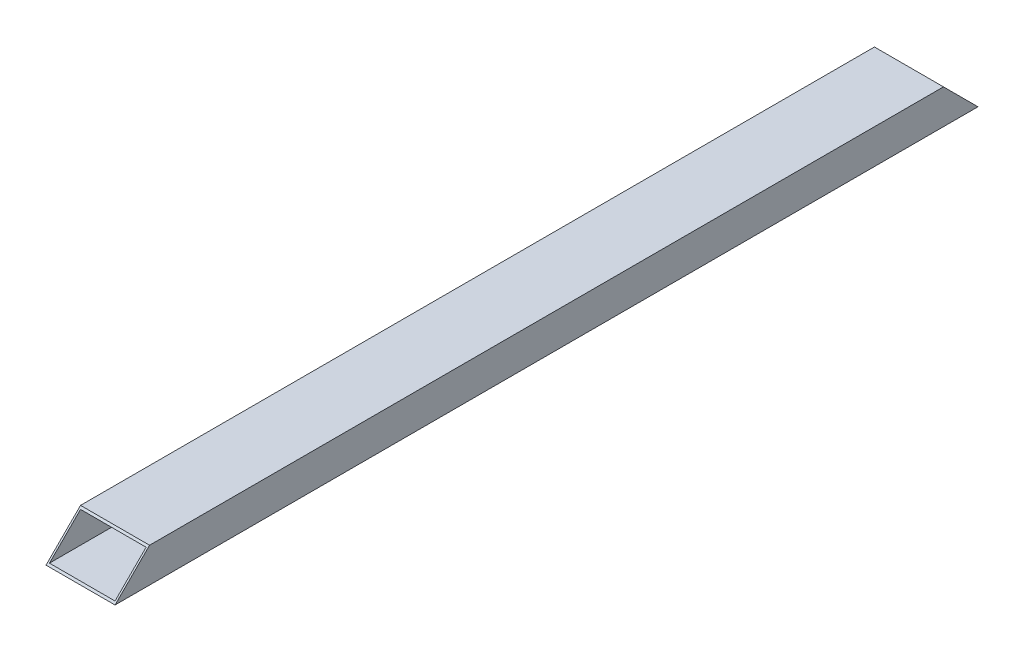
SolidWorks part; units mm, degrees
ref_plane "Front Plane" through (0, 0, 0) normal (0, 0, 1) x (1, 0, 0)
ref_plane "Top Plane" through (0, 0, 0) normal (0, 1, 0) x (1, 0, 0)
ref_plane "Right Plane" through (0, 0, 0) normal (1, 0, 0) x (0, 0, -1)
sketch "Sketch1" plane through (0, 0, 0) normal (0, 0, 1) x (1, 0, 0)
  line L0 (-27.5574, 0) -> (38.5818, 0) construction
  line L1 (0, 18.8259) -> (0, -17.5693) construction
  line L5 (20, -8) -> (-20, -8)
  line L8 (-20, -8) -> (-20, 12)
  line L9 (20, -8) -> (20, 12)
  line L10 (-20, 12) -> (20, 12)
  point P7 (0, -8)
  dimension "D1" = 40
  dimension "D2" = 40
  dimension "D3" = 20
extrude "Boss-Extrude1" add sketch "Sketch1" along normal blind 500
sketch "Sketch3" plane through (0, 0, 500) normal (0, 0, 1) x (1, 0, 0)
  line L16 (-19, -7) -> (19, -7)
  line L17 (-19, 11) -> (-19, -7)
  line L18 (19, -7) -> (19, 11)
  line L19 (19, 11) -> (-19, 11)
  line L20 (-19, -7) -> (19, -7)
  line L21 (-19, 11) -> (-19, -7)
  line L22 (19, -7) -> (19, 11)
  line L23 (19, 11) -> (-19, 11)
  dimension "D1" = 1
extrude "Cut-Extrude1" cut sketch "Sketch3" against normal through all
sketch "Sketch4" plane through (20, 0, 0) normal (1, 0, 0) x (0, 0, -1)
  line L0 (-500, 12) -> (-480, 12)
  line L1 (-500, 12) -> (0, 12) construction
  line L2 (-480, 12) -> (-500, -8)
  line L3 (-500, -8) -> (-500, 12)
  line L4 (0, 12) -> (-20, 12)
  line L5 (-20, 12) -> (0, -8)
  line L6 (0, -8) -> (0, 12)
  dimension "D1" = 20
  dimension "D2" = 20
  dimension "D3" = 20
  dimension "D4" = 20
extrude "Cut-Extrude2" cut sketch "Sketch4" against normal through all
